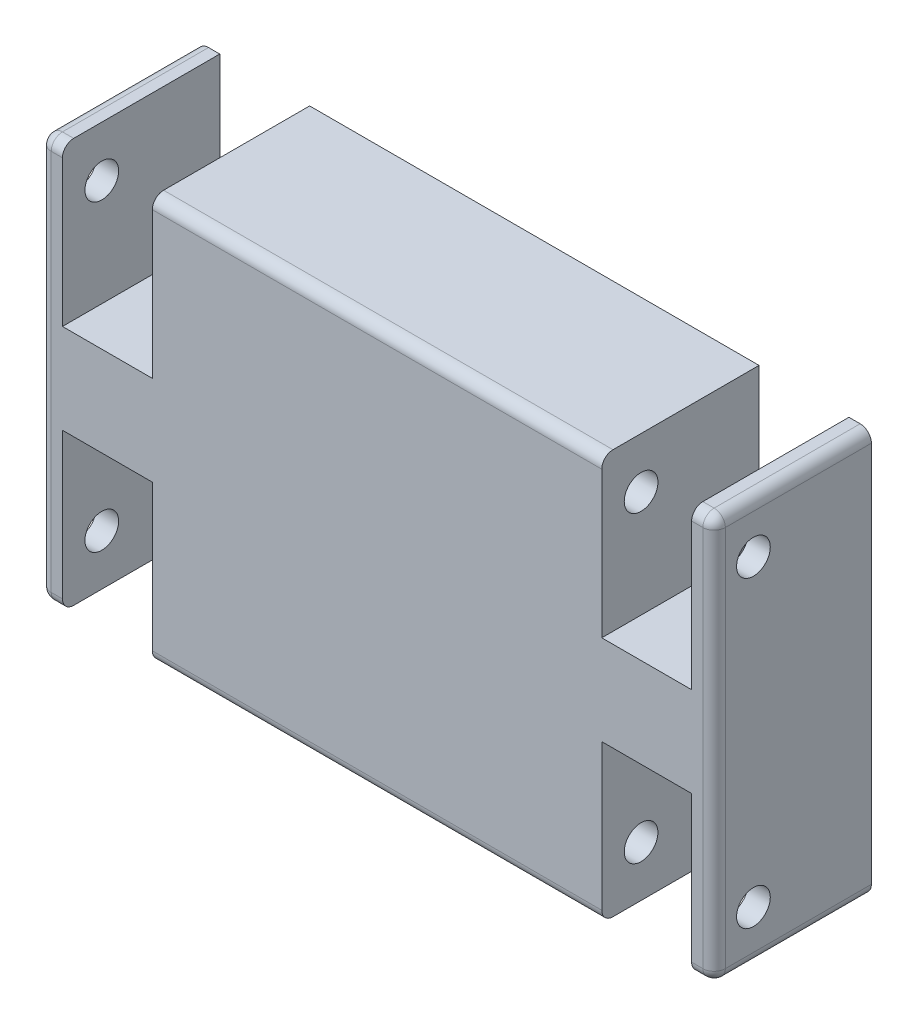
SolidWorks part; units mm, degrees
ref_plane "Alzado" through (0, 0, 0) normal (0, 0, 1) x (1, 0, 0)
ref_plane "Planta" through (0, 0, 0) normal (0, 1, 0) x (1, 0, 0)
ref_plane "Vista lateral" through (0, 0, 0) normal (1, 0, 0) x (0, 0, -1)
sketch "Croquis2" plane through (0, 0, 0) normal (0, 0, 1) x (1, 0, 0)
  line L1 (0, 0) -> (300, 0)
  line L2 (0, 0) -> (0, 180)
  line L3 (0, 180) -> (300, 180)
  line L4 (300, 0) -> (300, 180)
  dimension "D1" = 300
  dimension "D2" = 180
extrude "Saliente-Extruir3" add sketch "Croquis2" along normal blind 70
sketch "Croquis3" plane through (0, 0, 70) normal (0, 0, 1) x (1, 0, 0)
  line L0 (0, 90) -> (300, 90)
  line L1 (0, 180) -> (0, 0) construction
  line L2 (300, 0) -> (300, 180) construction
  line L3 (0, 0) -> (300, 0) construction
  line L4 (10, 0) -> (50, 0)
  line L5 (10, 0) -> (10, 70)
  line L6 (10, 70) -> (50, 70)
  line L7 (50, 0) -> (50, 70)
  line L8 (10, 0) -> (0, 0)
  line L9 (150, 90) -> (150, 0)
  line L10 (290, 0) -> (300, 0)
  line L11 (250, 0) -> (250, 70)
  line L12 (290, 70) -> (250, 70)
  line L13 (290, 0) -> (290, 70)
  line L14 (290, 0) -> (250, 0)
  line L15 (290, 180) -> (250, 180)
  line L16 (290, 180) -> (290, 110)
  line L17 (290, 110) -> (250, 110)
  line L18 (250, 180) -> (250, 110)
  line L19 (290, 180) -> (300, 180)
  line L20 (10, 180) -> (0, 180)
  line L21 (50, 180) -> (50, 110)
  line L22 (10, 110) -> (50, 110)
  line L23 (10, 180) -> (10, 110)
  line L24 (10, 180) -> (50, 180)
  line M9 (0, 0) -> (300, 0)
  line M11 (300, 180) -> (0, 180)
  dimension "D1" = 40
  dimension "D2" = 70
  dimension "D3" = 10
extrude "Cortar-Extruir1" cut sketch "Croquis3" against normal blind 70 contours L23 L22 L21 M11 | L13 L12 L11 M9 | L7 L6 L5 M9 | L16 L17 L18 L15
sketch "Croquis4" plane through (300, 0, 0) normal (1, 0, 0) x (0, 0, -1)
  line L0 (-70, 180) -> (-35, 135) construction
  line L1 (-70, 180) -> (-35, 180) construction
  line L2 (-70, 180) -> (-70, 135) construction
  line L3 (-70, 135) -> (-35, 135) construction
  line L4 (-35, 180) -> (-35, 135) construction
  line L5 (0, 90) -> (-70, 90) construction
  line L6 (0, 0) -> (0, 180) construction
  line L7 (-70, 0) -> (-70, 180) construction
  circle A0 centre (-52.5, 157.5) radius 7.5
  circle A1 centre (-52.5, 22.5) radius 7.5
  dimension "D3" = 15
  dimension "D1" = 45
  dimension "D2" = 35
extrude "Cortar-Extruir2" cut sketch "Croquis4" against normal blind 400
fillet "Redondeo2" radius 5 1 edges at (150, 0, 70)
fillet "Redondeo3" radius 5 1 edges at (150, 180, 70)
fillet "Redondeo4" radius 5 1 edges at (5, 180, 70)
fillet "Redondeo5" radius 5 1 edges at (295, 180, 70)
fillet "Redondeo6" radius 5 1 edges at (295, 0, 70)
fillet "Redondeo7" radius 5 1 edges at (5, 0, 70)
fillet "Redondeo8" radius 5 5 edges at (0, 90, 70) (0, 180, 32.5) (0, 178.5355, 68.5355) (0, 0, 32.5) (0, 1.4645, 68.5355)
fillet "Redondeo9" radius 5 5 edges at (300, 180, 32.5) (300, 178.5355, 68.5355) (300, 90, 70) (300, 0, 32.5) (300, 1.4645, 68.5355)
